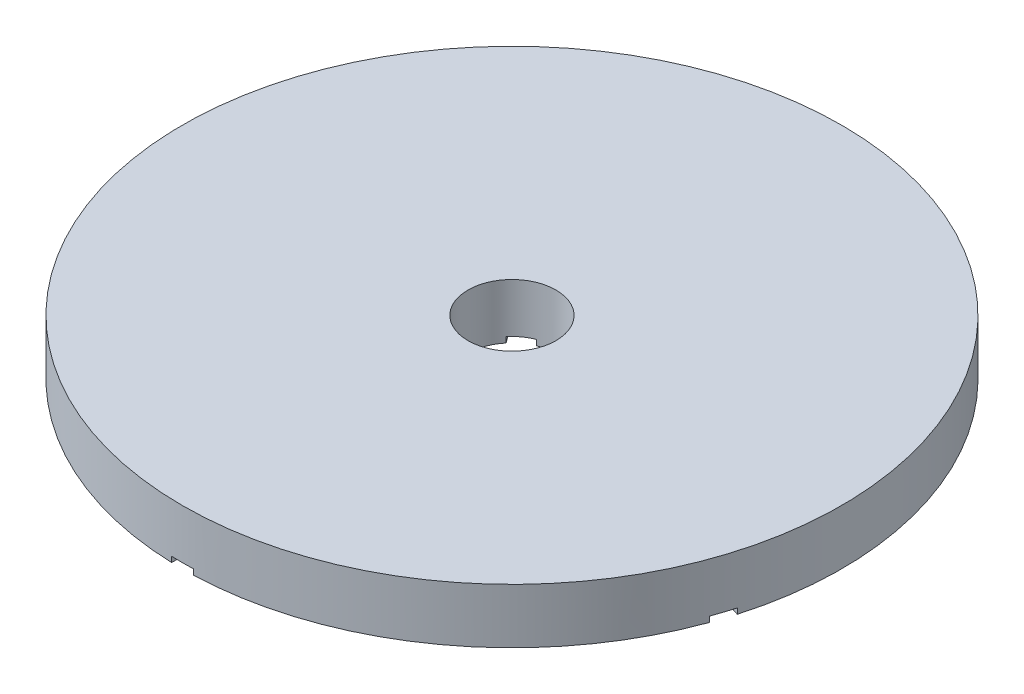
SolidWorks part; units mm, degrees
ref_plane "Front Plane" through (0, 0, 0) normal (0, 0, 1) x (1, 0, 0)
ref_plane "Top Plane" through (0, 0, 0) normal (0, 1, 0) x (1, 0, 0)
ref_plane "Right Plane" through (0, 0, 0) normal (1, 0, 0) x (0, 0, -1)
sketch "Sketch1" plane through (0, 0, 0) normal (0, 1, 0) x (1, 0, 0)
  circle A0 centre (0, 0) radius 15
extrude "Boss-Extrude1" add sketch "Sketch1" along normal blind 2.5
sketch "Sketch2" plane through (0, 0, 0) normal (0, 1, 0) x (1, 0, 0)
  line L0 (-0.5, 0) -> (0.5, 0)
  line L1 (0.5, 0) -> (0.5, -15)
  line L3 (-0.5, -15) -> (-0.5, 0)
  line L4 (-0.1545, 0.4755) -> (0.1545, -0.4755)
  line L5 (0.1545, -0.4755) -> (-14.1113, -5.1108)
  line L6 (-14.4204, -4.1597) -> (-0.1545, 0.4755)
  line L7 (0.4045, 0.2939) -> (-0.4045, -0.2939)
  line L8 (-0.4045, -0.2939) -> (-9.2213, 11.8414)
  line L9 (-8.4123, 12.4291) -> (0.4045, 0.2939)
  line L10 (0.4045, -0.2939) -> (-0.4045, 0.2939)
  line L11 (-0.4045, 0.2939) -> (8.4123, 12.4291)
  line L12 (9.2213, 11.8414) -> (0.4045, -0.2939)
  line L13 (-0.1545, -0.4755) -> (0.1545, 0.4755)
  line L14 (0.1545, 0.4755) -> (14.4204, -4.1597)
  line L15 (14.1113, -5.1108) -> (-0.1545, -0.4755)
  arc A0 (-0.5, -15) -> (0.5, -15) centre (0, 0) ccw
  arc A1 (-14.4204, -4.1597) -> (-14.1113, -5.1108) centre (0, 0) ccw
  arc A2 (-8.4123, 12.4291) -> (-9.2213, 11.8414) centre (0, 0) ccw
  arc A3 (9.2213, 11.8414) -> (8.4123, 12.4291) centre (0, 0) ccw
  arc A4 (14.1113, -5.1108) -> (14.4204, -4.1597) centre (0, 0) ccw
  point P4 (0, 0)
  point P13 (0, 0)
  point P19 (0, 0)
  point P25 (0, 0)
  point P31 (0, 0)
  point P34 (0, 0)
  dimension "D1" = 5
extrude "Cut-Extrude3" cut sketch "Sketch2" along normal blind 0.25 contours L15 L5 L4 L13 | L14 L9 L7 L0 L1 L12 | L12 L1 L0 L10 | L14 L13 L7 L9 | L13 L14 L9 L11 L6 L4 | L11 L10 L4 L6 | L10 L11 L6 L8 L3 L0 | L8 L7 L0 L3 | L5 L15 L13 L7 L8 L3 | L3 A0 L1 L15 L5 | L6 A1 L5 L3 L8 | L9 A2 L8 L6 L11 | L12 A3 L11 L9 L14
sketch "Sketch3" plane through (0, 0, 0) normal (0, 1, 0) x (1, 0, 0)
  circle A0 centre (0, 0) radius 2
extrude "Cut-Extrude4" cut sketch "Sketch3" along normal through all
